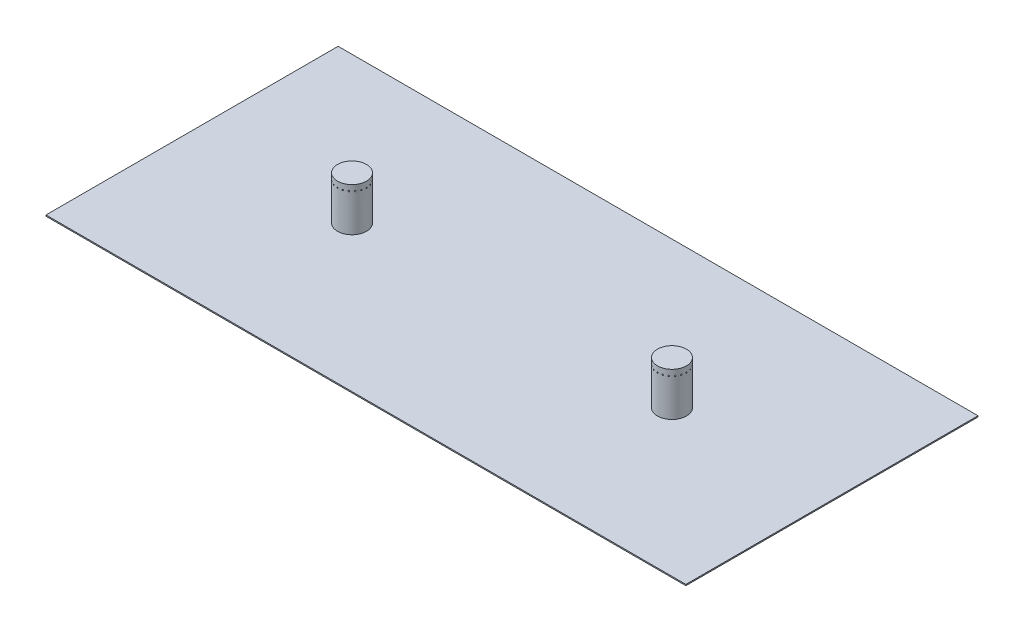
SolidWorks part; units mm, degrees
material "PVC Rigid"
ref_plane "Front Plane" through (0, 0, 0) normal (0, 0, 1) x (1, 0, 0)
ref_plane "Top Plane" through (0, 0, 0) normal (0, 1, 0) x (1, 0, 0)
ref_plane "Right Plane" through (0, 0, 0) normal (1, 0, 0) x (0, 0, -1)
sketch "Sketch1" plane through (0, 0, 0) normal (0, 1, 0) x (1, 0, 0)
  line L1 (-552, 252) -> (552, 252)
  line L2 (-552, 252) -> (-552, -252)
  line L3 (-552, -252) -> (552, -252)
  line L4 (552, 252) -> (552, -252)
  line L5 (-552, 252) -> (552, -252) construction
  line L6 (-552, -252) -> (552, 252) construction
  point P0 (0, 0)
extrude "Boss-Extrude1" add sketch "Sketch1" along normal blind 2
sketch "Sketch2" plane through (0, 2, 0) normal (0, 1, 0) x (1, 0, 0)
  line L0 (0, 0) -> (-552, 0) construction
  line L3 (-552, 252) -> (-552, -252) construction
  circle A0 centre (-276, 0) radius 25
  point P4 (-276, 0)
extrude "Boss-Extrude2" add sketch "Sketch2" along normal blind 75
ref_plane "Plane1" through (0, 0, 25) normal (0, 0, 1) x (1, 0, 0)
sketch "Sketch3" plane through (0, 0, 25) normal (0, 0, 1) x (1, 0, 0)
  line L0 (-301, 67) -> (-251, 67) construction
  line L1 (-301, 77) -> (-301, 2) construction
  line L2 (-251, 2) -> (-251, 77) construction
  line L3 (-251, 77) -> (-301, 77) construction
  circle A0 centre (-276, 67) radius 1
  dimension "D1" = 10
extrude "Cut-Extrude1" cut sketch "Sketch3" against normal blind 5 contours A0
pattern_circular "CirPattern1" count 20 over 360 about axis through (-276, 0, 0) along (0, 1, 0) of "Cut-Extrude1"
mirror "Mirror1" about plane through (0, 0, 0) normal (1, 0, 0) of "Boss-Extrude2"
mirror "Mirror2" about plane through (0, 0, 0) normal (1, 0, 0) of "CirPattern1", "Cut-Extrude1"
